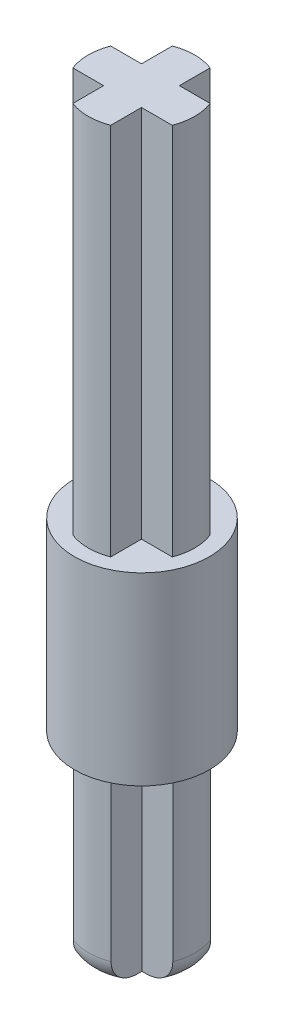
SolidWorks part; units mm, degrees
ref_plane "Front Plane" through (0, 0, 0) normal (0, 0, 1) x (1, 0, 0)
ref_plane "Top Plane" through (0, 0, 0) normal (0, 1, 0) x (1, 0, 0)
ref_plane "Right Plane" through (0, 0, 0) normal (1, 0, 0) x (0, 0, -1)
sketch "Sketch1" plane through (0, 0, 0) normal (0, 1, 0) x (1, 0, 0)
  line L0 (-0.8, -0.8) -> (-0.8, -2.103)
  line L1 (-0.8, 0.8) -> (-2.103, 0.8)
  line L2 (2.103, 0.8) -> (0.8, 0.8)
  line L3 (2.103, -0.8) -> (0.8, -0.8)
  line L4 (0.8, -0.8) -> (0.8, -2.103)
  line L5 (-0.8, -0.8) -> (-2.103, -0.8)
  line L6 (-7.75, 0) -> (-7.75, 0)
  line L7 (-7.75, 0) -> (-7.75, 0)
  line L8 (-0.8, 2.103) -> (-0.8, 0.8)
  line L9 (0.8, 2.103) -> (0.8, 0.8)
  line L10 (-7.75, 0) -> (-7.75, 0)
  line L11 (7.75, 0) -> (7.75, 0)
  line L12 (7.75, 0) -> (7.75, 0)
  line L13 (7.75, 0) -> (7.75, 0)
  line L14 (7.75, 0) -> (7.75, 0)
  line L15 (-7.75, 0) -> (-7.75, 0)
  line L16 (-8.6621, 8.6621) -> (-8.6621, 8.6621)
  line L17 (-8.6621, -8.6621) -> (-8.6621, -8.6621)
  line L18 (-8.6621, -8.6621) -> (-8.6621, -8.6621)
  line L19 (8.6621, -8.6621) -> (8.6621, -8.6621)
  line L20 (8.6621, -8.6621) -> (8.6621, -8.6621)
  line L21 (8.6621, 8.6621) -> (8.6621, 8.6621)
  line L22 (8.6621, 8.6621) -> (8.6621, 8.6621)
  line L23 (-8.6621, 8.6621) -> (-8.6621, 8.6621)
  arc A0 (-2.103, 0.8) -> (-2.103, -0.8) centre (0, 0) ccw
  arc A1 (0.8, 2.103) -> (-0.8, 2.103) centre (0, 0) ccw
  arc A2 (2.103, -0.8) -> (2.103, 0.8) centre (0, 0) ccw
  arc A3 (-0.8, -2.103) -> (0.8, -2.103) centre (0, 0) ccw
  arc A4 (-7.75, 0) -> (-7.75, 0) centre (-7.75, 0) ccw
  arc A5 (-7.75, 0) -> (7.75, 0) centre (0, 0) ccw
  arc A6 (7.75, 0) -> (7.75, 0) centre (7.75, 0) ccw
  arc A7 (7.75, 0) -> (-7.75, 0) centre (0, 0) ccw
  arc A8 (-8.6621, 8.6621) -> (-8.6621, -8.6621) centre (0, 0) ccw
  arc A9 (-8.6621, -8.6621) -> (8.6621, -8.6621) centre (0, 0) ccw
  arc A10 (8.6621, -8.6621) -> (8.6621, 8.6621) centre (0, 0) ccw
  arc A11 (8.6621, 8.6621) -> (-8.6621, 8.6621) centre (0, 0) ccw
  point P26 (0.8, 0)
  dimension "D1" = 4.5
  dimension "D2" = 10
  dimension "D3" = 10
extrude "Boss-Extrude1" add sketch "Sketch1" along normal offset from surface (15.8 mm away) 15.8 contours L0 A3 L4 L3 A2 L2 L9 A1 L8 L1 A0 L5 up to plane "Top Plane"
fillet "Fillet1" radius 1 1 edges at (-2.25, 0, 0)
fillet "Fillet2" radius 1 1 edges at (0, 0, 2.25)
fillet "Fillet3" radius 1 1 edges at (2.25, 0, 0)
fillet "Fillet4" radius 1 1 edges at (0, 0, -2.25)
sketch "Sketch3" plane through (0, 15.8, 0) normal (0, 1, 0) x (1, 0, 0)
  circle A0 centre (0, 0) radius 2.85
  dimension "D1" = 5.7
extrude "Boss-Extrude2" add sketch "Sketch3" against normal blind 7.8 contours A0
sketch "Sketch6" plane through (0, 15.8, 0) normal (0, 1, 0) x (1, 0, 0)
  line L0 (0, 2.85) -> (0, 0) construction
  line L1 (-0.8286, -0.7912) -> (-0.8286, -2.0942)
  line L2 (-0.8286, 0.8088) -> (-2.1315, 0.8088)
  line L3 (2.0744, 0.8088) -> (0.7714, 0.8088)
  line L4 (2.0744, -0.7912) -> (0.7714, -0.7912)
  line L5 (0.7714, -0.7912) -> (0.7714, -2.0942)
  line L6 (-0.8286, -0.7912) -> (-2.1315, -0.7912)
  line L7 (-0.8286, 2.1118) -> (-0.8286, 0.8088)
  line L8 (0.7714, 2.1118) -> (0.7714, 0.8088)
  circle A0 centre (0, 0) radius 2.85 construction
  arc A2 (-2.1315, 0.8088) -> (-2.1315, -0.7912) centre (-0.0286, 0.0088) ccw
  arc A3 (0.7714, 2.1118) -> (-0.8286, 2.1118) centre (-0.0286, 0.0088) ccw
  arc A4 (2.0744, -0.7912) -> (2.0744, 0.8088) centre (-0.0286, 0.0088) ccw
  arc A5 (-0.8286, -2.0942) -> (0.7714, -2.0942) centre (-0.0286, 0.0088) ccw
  point P25 (0.7714, 0.0088)
extrude "Boss-Extrude4" add sketch "Sketch6" along normal blind 15.8
